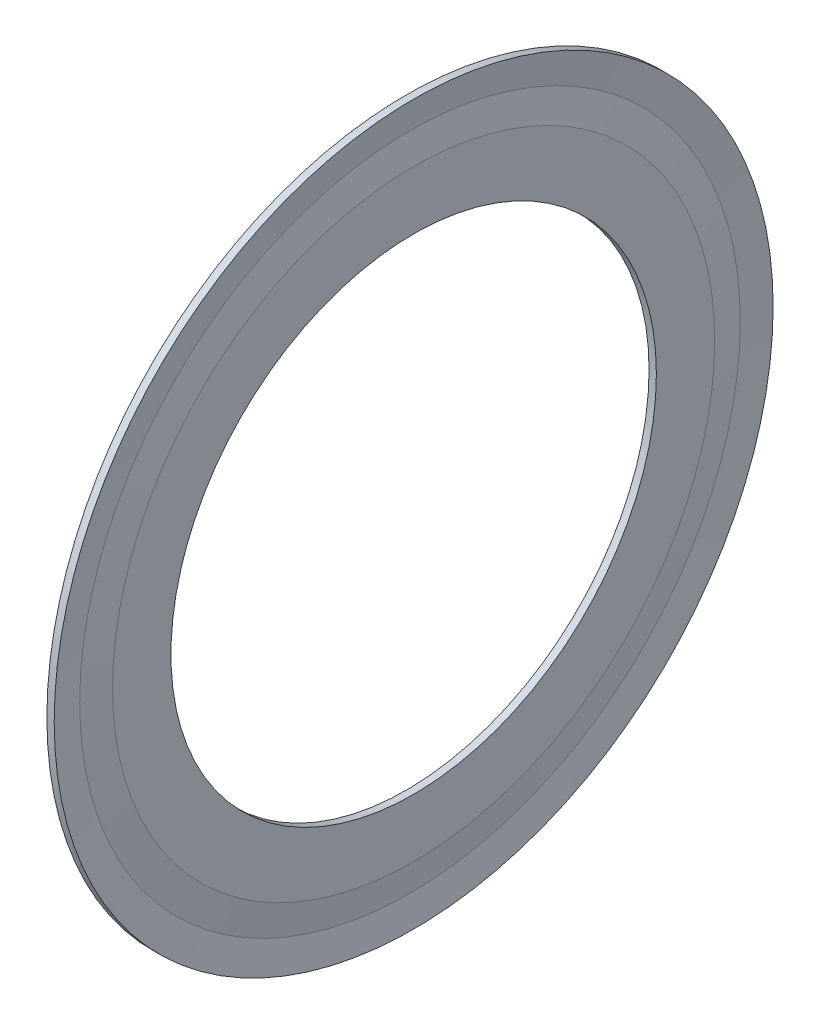
SolidWorks part; units mm, degrees
ref_plane "Front Plane" through (0, 0, 0) normal (0, 0, 1) x (1, 0, 0)
ref_plane "Top Plane" through (0, 0, 0) normal (0, 1, 0) x (1, 0, 0)
ref_plane "Right Plane" through (0, 0, 0) normal (1, 0, 0) x (0, 0, -1)
ref_plane "Plane1" through (0, 0, 0) normal (0, 0, 1) x (1, 0, 0)
sketch "Sketch1" plane through (0, 0, 0) normal (0, 0, 1) x (1, 0, 0)
  line L0 (2.7317, 3.0392) -> (2.8057, 2.45)
  line L1 (2.8057, 2.45) -> (2.8796, 2.45)
  line L2 (2.8796, 2.45) -> (2.8796, 3.0392)
  line L3 (2.8796, 3.0392) -> (2.8426, 3.3339)
  line L4 (2.8426, 3.3339) -> (2.8796, 3.6285)
  line L5 (2.8796, 3.6285) -> (2.8057, 3.6285)
  line L6 (2.8057, 3.6285) -> (2.7317, 3.32)
  line L7 (2.7317, 3.32) -> (2.7317, 3.0392)
  line L8 (31.0127, 0) -> (-31.0127, 0) construction
  dimension "D1" = 2.45
revolve "Revolve1" add sketch "Sketch1" angle 360 about L8
